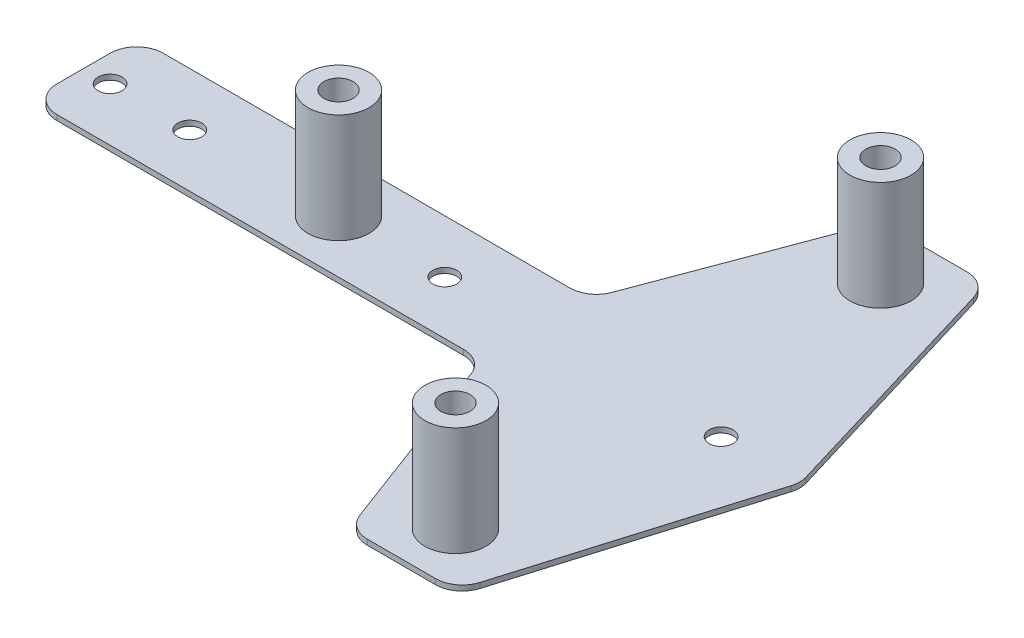
SolidWorks part; units mm, degrees
ref_plane "Front Plane" through (0, 0, 0) normal (0, 0, 1) x (1, 0, 0)
ref_plane "Top Plane" through (0, 0, 0) normal (0, 1, 0) x (1, 0, 0)
ref_plane "Right Plane" through (0, 0, 0) normal (1, 0, 0) x (0, 0, -1)
sketch "Sketch1" plane through (0, 0, 0) normal (0, 1, 0) x (1, 0, 0)
  line L0 (-55, 10) -> (6.535, 10)
  line L1 (11.2166, 13.2444) -> (23.7834, 46.7556)
  line L2 (28.465, 50) -> (41.2798, 50)
  line L3 (46.069, 46.4367) -> (59.569, 1.4367)
  line L4 (59.569, -1.4367) -> (46.069, -46.4367)
  line L5 (41.2798, -50) -> (28.465, -50)
  line L6 (23.7834, -46.7556) -> (11.2166, -13.2444)
  line L7 (6.535, -10) -> (-55, -10)
  line L8 (-60, -5) -> (-60, 5)
  line L9 (-60, 0) -> (60, 0) construction
  line L10 (10, -10) -> (10, 10) construction
  line L11 (25, 50) -> (25, -50) construction
  line L12 (45, -50) -> (45, 50) construction
  arc A0 (6.535, 10) -> (11.2166, 13.2444) centre (6.535, 15) ccw
  arc A1 (23.7834, 46.7556) -> (28.465, 50) centre (28.465, 45) cw
  arc A2 (41.2798, 50) -> (46.069, 46.4367) centre (41.2798, 45) cw
  arc A3 (59.569, 1.4367) -> (59.569, -1.4367) centre (54.7798, 0) cw
  arc A4 (46.069, -46.4367) -> (41.2798, -50) centre (41.2798, -45) cw
  arc A5 (28.465, -50) -> (23.7834, -46.7556) centre (28.465, -45) cw
  arc A6 (11.2166, -13.2444) -> (6.535, -10) centre (6.535, -15) ccw
  arc A7 (-55, -10) -> (-60, -5) centre (-55, -5) cw
  arc A8 (-55, 10) -> (-60, 5) centre (-55, 5) ccw
  point P10 (25, 0)
  point P36 (-60, -10)
  point P39 (-60, 10)
  dimension "D7" = 5
  dimension "D1" = 20
  dimension "D2" = 70
  dimension "D3" = 15
  dimension "D4" = 20
  dimension "D5" = 15
  dimension "D6" = 100
extrude "Boss-Extrude1" add sketch "Sketch1" along normal blind 1
sketch "Sketch2" plane through (0, 1, 0) normal (0, 1, 0) x (1, 0, 0)
  line L0 (-27, 0) -> (0, 0) construction
  line L1 (0, 0) -> (35, 0) construction
  line L2 (35, 40) -> (35, -40) construction
  circle A0 centre (-27, 0) radius 2.75
  circle A1 centre (35, 40) radius 2.75
  circle A2 centre (35, -40) radius 2.75
  dimension "D4" = 5.5
  dimension "D1" = 62
  dimension "D2" = 35
  dimension "D3" = 80
extrude "Cut-Extrude1" cut sketch "Sketch2" against normal through all
sketch "Sketch3" plane through (0, 1, 0) normal (0, 1, 0) x (1, 0, 0)
  circle A0 centre (35, -40) radius 2.75 construction
  circle A1 centre (-27, 0) radius 2.75 construction
  circle A2 centre (35, 40) radius 2.75 construction
  circle A3 centre (35, -40) radius 2.75
  circle A4 centre (-27, 0) radius 2.75
  circle A5 centre (35, 40) radius 2.75
  circle A6 centre (-27, 0) radius 5.75
  circle A7 centre (35, 40) radius 5.75
  circle A8 centre (35, -40) radius 5.75
  dimension "D1" = 3
extrude "Boss-Extrude2" add sketch "Sketch3" along normal blind 20.5
sketch "Sketch4" plane through (0, 1, 0) normal (0, 1, 0) x (1, 0, 0)
  line L0 (-55, 0) -> (0, 0) construction
  line L1 (0, 0) -> (45, 0) construction
  circle A0 centre (-55, 0) radius 2.25
  circle A1 centre (45, 0) radius 2.25
  circle A3 centre (-7, 0) radius 2.25
  arc A4 (59.569, -1.4367) -> (59.569, 1.4367) centre (54.7798, 0) ccw construction
  dimension "D2" = 4.5
  dimension "D3" = 9.7798
  dimension "D1" = 52
  dimension "D4" = 100
extrude "Cut-Extrude2" cut sketch "Sketch4" against normal through all
sketch "Sketch5" plane through (0, 0, 0) normal (0, 1, 0) x (1, 0, 0)
  line L1 (-55, 10) -> (-70, 10)
  line L2 (-55, 10) -> (-55, -10)
  line L3 (-55, -10) -> (-70, -10)
  line L4 (-75, 5) -> (-75, -5)
  line L5 (-55, -10) -> (6.535, -10) construction
  line L6 (-60, 5) -> (-60, -5) construction
  line L7 (-70, 0) -> (-55, 0) construction
  arc A0 (-70, 10) -> (-75, 5) centre (-70, 5) ccw
  arc A1 (-70, -10) -> (-75, -5) centre (-70, -5) cw
  circle A2 centre (-70, 0) radius 2.25
  circle A3 centre (-55, 0) radius 2.25 construction
  dimension "D2" = 5
  dimension "D1" = 15
  dimension "D3" = 15
extrude "Boss-Extrude3" add sketch "Sketch5" along normal up to surface (1 mm away) up to face at (-55, 1, 2.25)
sketch "Sketch6" plane through (0, 1, 0) normal (0, 1, 0) x (1, 0, 0)
  line L0 (-55, -2.25) -> (-55, 2.25) construction
  circle A0 centre (-55, 0) radius 2.25
  arc A1 (-55, -2.25) -> (-55, 2.25) centre (-55, 0) ccw construction
extrude "Cut-Extrude3" cut sketch "Sketch6" against normal through all
